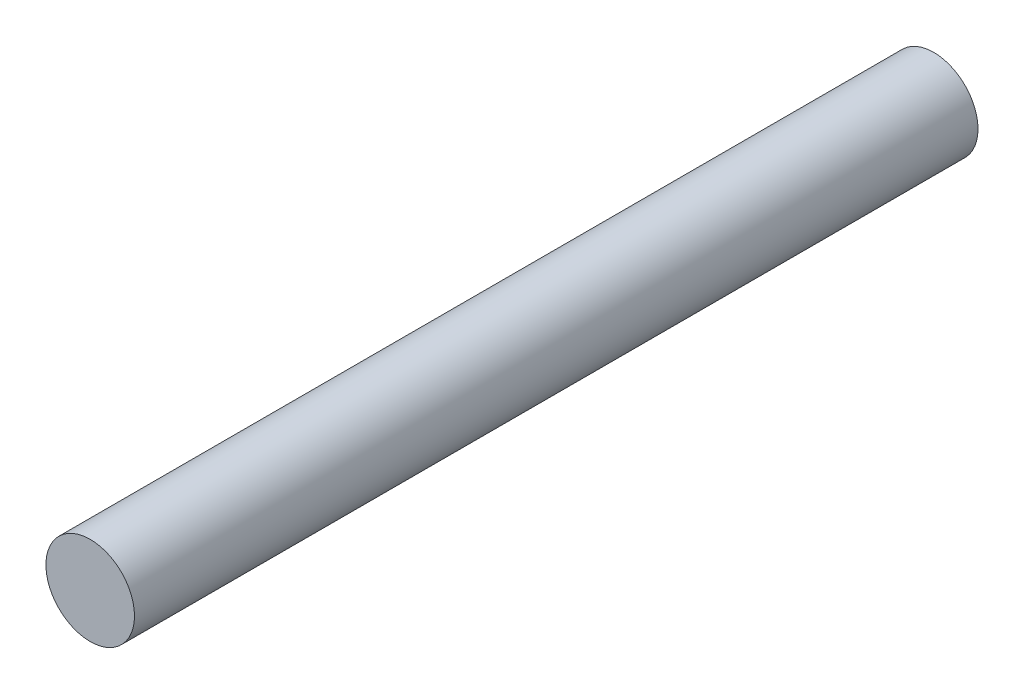
SolidWorks part; units mm, degrees
ref_plane "Front Plane" through (0, 0, 0) normal (0, 0, 1) x (1, 0, 0)
ref_plane "Top Plane" through (0, 0, 0) normal (0, 1, 0) x (1, 0, 0)
ref_plane "Right Plane" through (0, 0, 0) normal (1, 0, 0) x (0, 0, -1)
sketch "Sketch1" plane through (0, 0, 0) normal (0, 0, 1) x (1, 0, 0)
  circle A0 centre (0, 0) radius 1.05
  dimension "D1" = 2.1
extrude "Boss-Extrude1" add sketch "Sketch1" along normal blind 20
